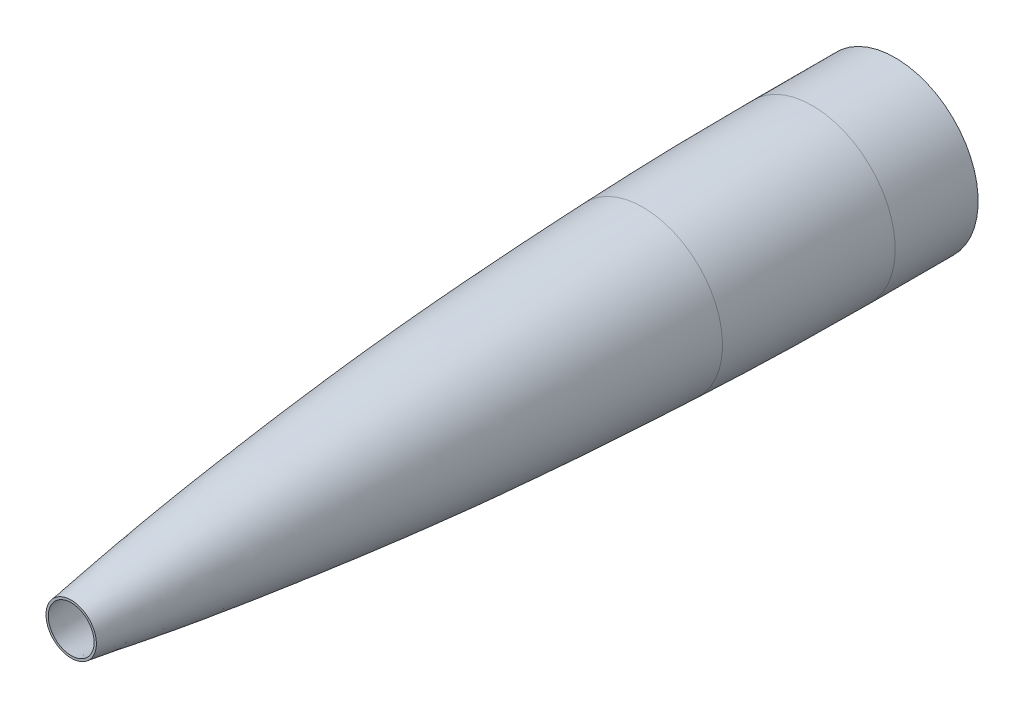
SolidWorks part; units mm, degrees
material "S-Glass Fiber"
ref_plane "Front Plane" through (0, 0, 0) normal (0, 0, 1) x (1, 0, 0)
ref_plane "Top Plane" through (0, 0, 0) normal (0, 1, 0) x (1, 0, 0)
ref_plane "Right Plane" through (0, 0, 0) normal (1, 0, 0) x (0, 0, -1)
sketch "Sketch1" plane through (0, 0, 0) normal (0, 1, 0) x (1, 0, 0)
  line L3 (78.359, 657.5952) -> (78.359, 788.9011)
  line L4 (78.359, 788.9011) -> (0, 788.9011)
  line L5 (0, 788.9011) -> (0, 0)
  line L6 (24.13, 0) -> (0, 0)
  line L7 (0, 64.5843) -> (31.75, 64.5843)
  line L8 (31.75, 64.5843) -> (33.8855, 64.2664)
  arc A1 (76.2, 547.3252) -> (78.359, 657.5952) centre (-2738.7178, 657.5952) ccw
  spline S0 degree 5 poles (18.923, -41.7414) (30.7792, 69.4117) (42.6354, 60.5621) (54.4916, 290.4246) (66.3479, 251.385) (78.2041, 602.4557) knots 0 0 0 0 0 0 1 1 1 1 1 1 construction
  spline S1 degree 5 poles (24.13, 0) (34.544, 73.2277) (44.958, 112.3911) (55.372, 268.074) (65.786, 281.4818) (76.2, 547.3252) knots 0.087836 0.087836 0.087836 0.087836 0.087836 0.087836 0.966194 0.966194 0.966194 0.966194 0.966194 0.966194
  dimension "D1" = 24.13
  dimension "D2" = 76.2
  dimension "D3" = 788.9011
  dimension "D4" = 78.359
  dimension "D5" = 2.159
  dimension "D6" = 31.75
  dimension "D7" = 64.5843
revolve "Revolve1" add sketch "Sketch1" angle 360 about L5
shell "Shell1" thickness 2.159
sketch "Sketch2" plane through (0, 0, 0) normal (0, 1, 0) x (1, 0, 0)
  line L0 (0, 788.9011) -> (0, 0) construction
  line L1 (24.13, 0) -> (0, 0) construction
  line L2 (78.359, 657.5952) -> (78.359, 788.9011) construction
  line L3 (0, 788.9011) -> (0, 0)
  line L4 (24.13, 0) -> (0, 0)
  line L5 (78.359, 657.5952) -> (78.359, 788.9011)
  line L6 (79.375, 709.487) -> (79.375, 788.9011)
  line L7 (79.375, 788.9011) -> (78.359, 788.9011)
  arc A0 (76.2, 547.3252) -> (78.359, 657.5952) centre (-2738.7178, 657.5952) ccw construction
  arc A1 (76.2, 547.3252) -> (78.359, 657.5952) centre (-2738.7178, 657.5952) ccw
  arc A2 (76.2, 547.3252) -> (79.375, 709.487) centre (-4063.3851, 709.487) ccw
  spline S0 degree 5 poles (-14.9108, -1999.4418) (8.4864, 1841.0903) (31.8835, -1946.3589) (55.2807, 2083.9119) (78.6779, -1357.7679) (102.075, 2547.0126) knots -0.570735 -0.570735 -0.570735 -0.570735 -0.570735 -0.570735 1.402674 1.402674 1.402674 1.402674 1.402674 1.402674 only from (24.13, 0) to (76.2, 547.3252) construction
  spline S1 degree 5 poles (24.13, 0) (34.544, 73.2277) (44.958, 112.3911) (55.372, 268.074) (65.786, 281.4818) (76.2, 547.3252) knots 0.087836 0.087836 0.087836 0.087836 0.087836 0.087836 0.966194 0.966194 0.966194 0.966194 0.966194 0.966194
  dimension "D1" = 79.375
revolve "Revolve2" add sketch "Sketch2" angle 360 about L3
